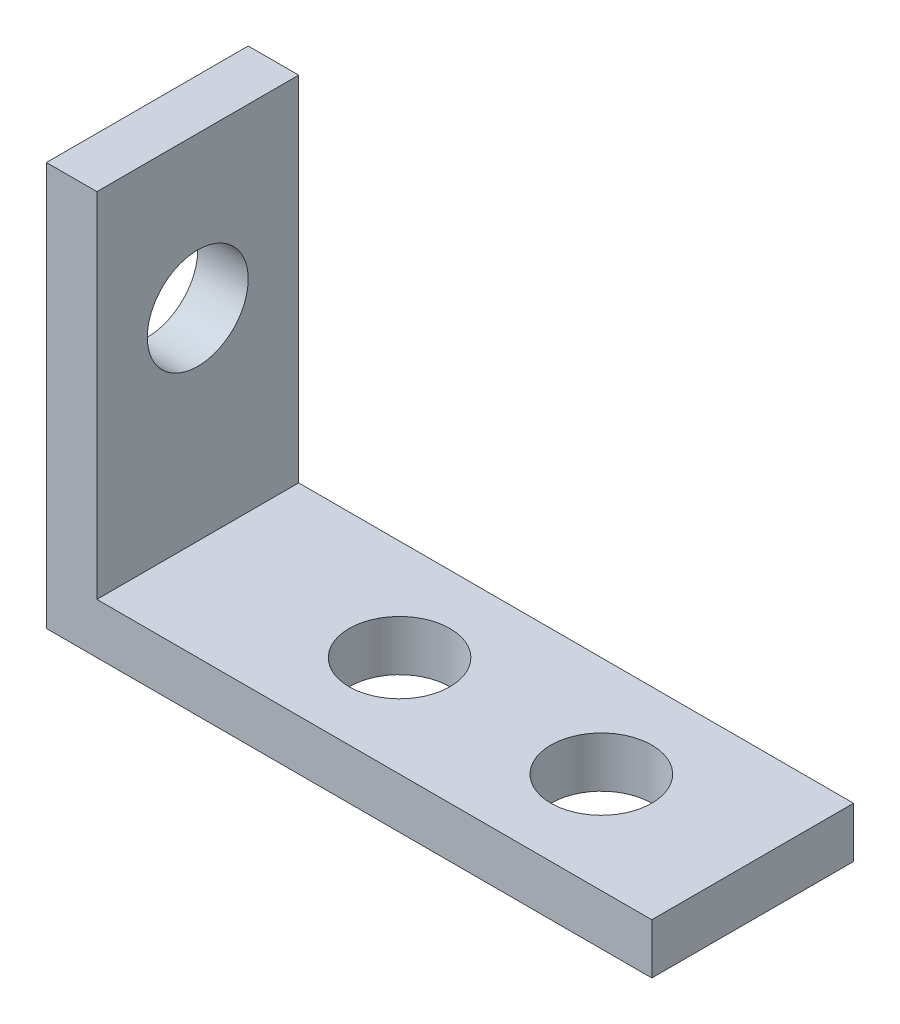
SolidWorks part; units mm, degrees
ref_plane "Front Plane" through (0, 0, 0) normal (0, 0, 1) x (1, 0, 0)
ref_plane "Top Plane" through (0, 0, 0) normal (0, 1, 0) x (1, 0, 0)
ref_plane "Right Plane" through (0, 0, 0) normal (1, 0, 0) x (0, 0, -1)
sketch "Sketch1" plane through (0, 0, 0) normal (0, 0, 1) x (1, 0, 0)
  line L0 (0, 0) -> (0, 25.4)
  line L1 (0, 25.4) -> (3.175, 25.4)
  line L2 (3.175, 25.4) -> (3.175, 3.175)
  line L3 (3.175, 3.175) -> (38.1, 3.175)
  line L4 (38.1, 3.175) -> (38.1, 0)
  line L5 (38.1, 0) -> (0, 0)
  dimension "D1" = 3.175
  dimension "D2" = 3.175
  dimension "D3" = 38.1
  dimension "D4" = 25.4
extrude "Boss-Extrude1" add sketch "Sketch1" along normal blind 12.7
sketch "Sketch2" plane through (0, 3.175, 0) normal (0, 1, 0) x (1, 0, 0)
  line L0 (38.1, -6.35) -> (3.175, -6.35) construction
  line L1 (38.1, -12.7) -> (38.1, 0) construction
  line L2 (3.175, -12.7) -> (3.175, 0) construction
  line L3 (0, -12.7) -> (0, 0) construction
  circle A0 centre (15.875, -6.35) radius 3.175
  circle A1 centre (28.575, -6.35) radius 3.175
  dimension "D1" = 6.35
  dimension "D3" = 15.875
  dimension "D2" = 12.7
extrude "Cut-Extrude1" cut sketch "Sketch2" against normal through all
sketch "Sketch3" plane through (3.175, 0, 0) normal (1, 0, 0) x (0, 0, -1)
  line L0 (-6.35, 25.4) -> (-6.35, 3.175) construction
  line L1 (-12.7, 25.4) -> (0, 25.4) construction
  line L2 (-12.7, 3.175) -> (0, 3.175) construction
  line L3 (-12.7, 0) -> (0, 0) construction
  circle A0 centre (-6.35, 28.575) radius 3.175
  circle A1 centre (-6.35, 15.875) radius 3.175
  dimension "D1" = 6.35
  dimension "D2" = 12.7
  dimension "D3" = 15.875
extrude "Cut-Extrude2" cut sketch "Sketch3" against normal through all
